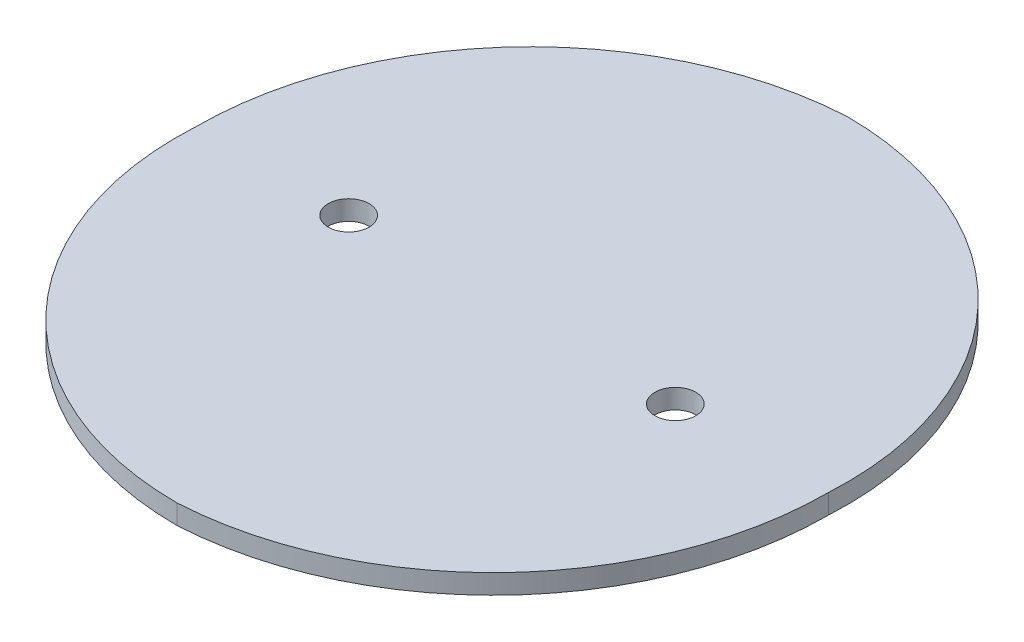
SolidWorks part; units mm, degrees
ref_plane "Front Plane" through (0, 0, 0) normal (0, 0, 1) x (1, 0, 0)
ref_plane "Top Plane" through (0, 0, 0) normal (0, 1, 0) x (1, 0, 0)
ref_plane "Right Plane" through (0, 0, 0) normal (1, 0, 0) x (0, 0, -1)
sketch "Sketch1" plane through (0, 0, 0) normal (0, 1, 0) x (1, 0, 0)
  arc A0 (-96.9, 0) -> (0, 102.5) centre (5.7618, 0) cw
  arc A1 (0, 102.5) -> (96.9, 0) centre (0, 5.447) cw
  arc A2 (96.9, 0) -> (0, -102.5) centre (-5.7618, 0) cw
  arc A3 (0, -102.5) -> (-96.9, 0) centre (0, -5.447) cw
  point P6 (0, 0)
  dimension "D1" = 102.5
  dimension "D2" = 96.9
extrude "Boss-Extrude1" add sketch "Sketch1" along normal mid plane 6
sketch "Sketch2" plane through (0, 3, 0) normal (0, 1, 0) x (1, 0, 0)
  circle A0 centre (-50, 0) radius 6.25
  circle A1 centre (50, 0) radius 6.25
  dimension "D1" = 6.25
  dimension "D2" = 50
  dimension "D3" = 50
extrude "Cut-Extrude1" cut sketch "Sketch2" against normal blind 6
